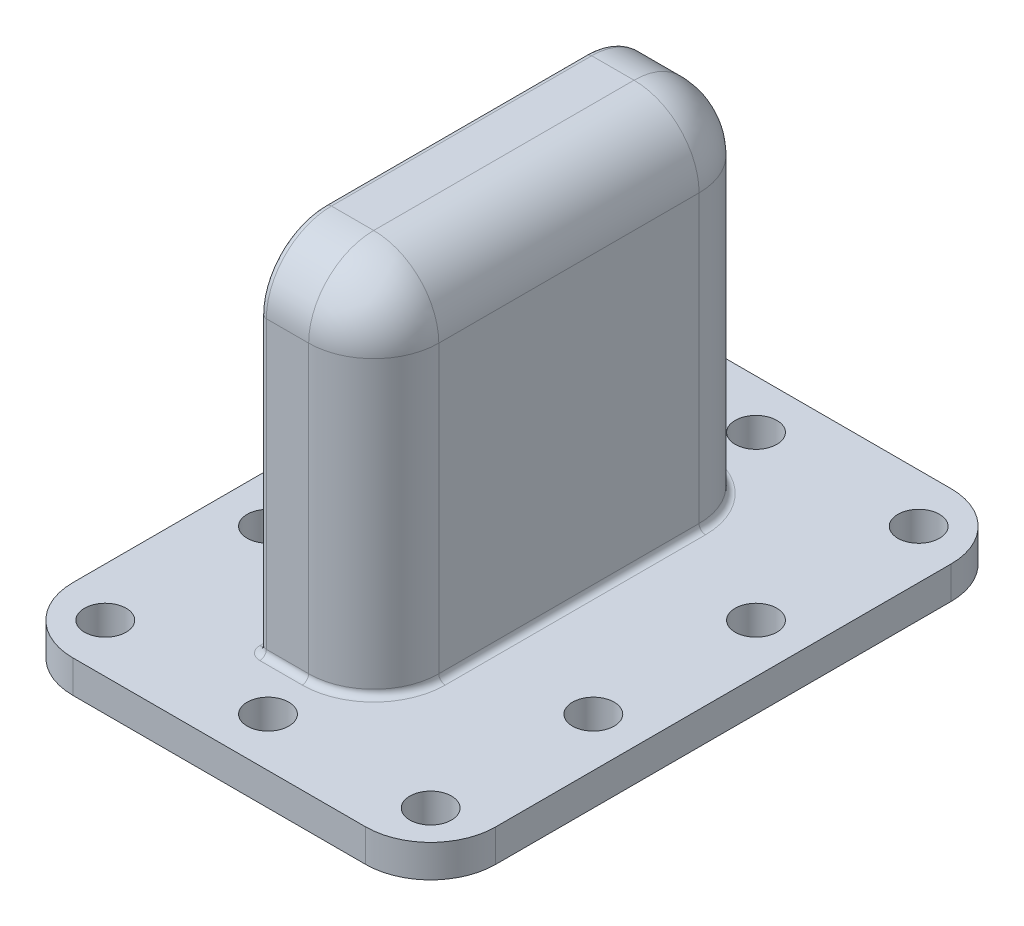
SolidWorks part; units mm, degrees
ref_plane "정면" through (0, 0, 0) normal (0, 0, 1) x (1, 0, 0)
ref_plane "윗면" through (0, 0, 0) normal (0, 1, 0) x (1, 0, 0)
ref_plane "우측면" through (0, 0, 0) normal (1, 0, 0) x (0, 0, -1)
sketch "스케치1" plane through (0, 0, 0) normal (0, 1, 0) x (1, 0, 0)
  line L0 (-25, 0) -> (25, 0) construction
  line L1 (-32.5, 32.5) -> (32.5, 32.5)
  line L2 (-32.5, 32.5) -> (-32.5, -57.5)
  line L3 (-32.5, -57.5) -> (32.5, -57.5)
  line L4 (32.5, 32.5) -> (32.5, -57.5)
  circle A0 centre (-25, 25) radius 3.2
  circle A1 centre (25, 25) radius 3.2
  circle A2 centre (25, 0) radius 3.2
  circle A3 centre (-25, 0) radius 3.2
  circle A4 centre (25, -50) radius 3.2
  circle A5 centre (-25, -50) radius 3.2
  circle A6 centre (0, 25) radius 3.2
  circle A7 centre (0, -50) radius 3.2
  circle A8 centre (25, -25) radius 3.2
  circle A9 centre (-25, -25) radius 3.2
  point P12 (0, 0)
  point P23 (0, 0)
  point P24 (0, 0)
  point P25 (0, 0)
  dimension "D1" = 6.4
  dimension "D2" = 50
  dimension "D3" = 25
  dimension "D4" = 50
  dimension "D5" = 7.5
  dimension "D6" = 7.5
  dimension "D7" = 7.5
  dimension "D8" = 7.5
  dimension "D9" = 25
extrude "보스-돌출1" add sketch "스케치1" along normal blind 5
sketch "스케치2" plane through (0, 5, 0) normal (0, 1, 0) x (1, 0, 0)
  line L0 (32.5, 32.5) -> (-32.5, 32.5) construction
  line L1 (-8.75, 17.5) -> (8.75, 17.5)
  line L2 (-8.75, 17.5) -> (-8.75, -42.5)
  line L3 (-8.75, -42.5) -> (8.75, -42.5)
  line L4 (8.75, 17.5) -> (8.75, -42.5)
  line L7 (-32.5, -57.5) -> (32.5, -57.5) construction
  point P4 (0, 17.5)
  dimension "D1" = 17.5
  dimension "D2" = 15
  dimension "D3" = 15
fillet "필렛1" radius 10 4 edges at (32.5, 2.5, 57.5) (-32.5, 2.5, 57.5) (-32.5, 2.5, -32.5) (32.5, 2.5, -32.5)
extrude "보스-돌출2" add sketch "스케치2" along normal offset from surface (55 mm away) 60 up to face at (0, 0, 12.5)
fillet "필렛2" radius 10 5 edges at (8.75, 60, 12.5) (8.75, 32.5, -17.5) (8.75, 32.5, 42.5) (0, 60, -17.5) (0, 60, 42.5)
fillet "필렛3" radius 1 11 edges at (8.75, 5, 12.5) (5.8211, 5, -14.5711) (5.8211, 5, 39.5711) (-5, 5, -17.5) (-5, 5, 42.5) (-8.75, 27.5, -17.5) (-8.75, 57.0711, -14.5711) (-8.75, 60, 12.5) (-8.75, 5, 12.5) (-8.75, 57.0711, 39.5711) (-8.75, 27.5, 42.5)
